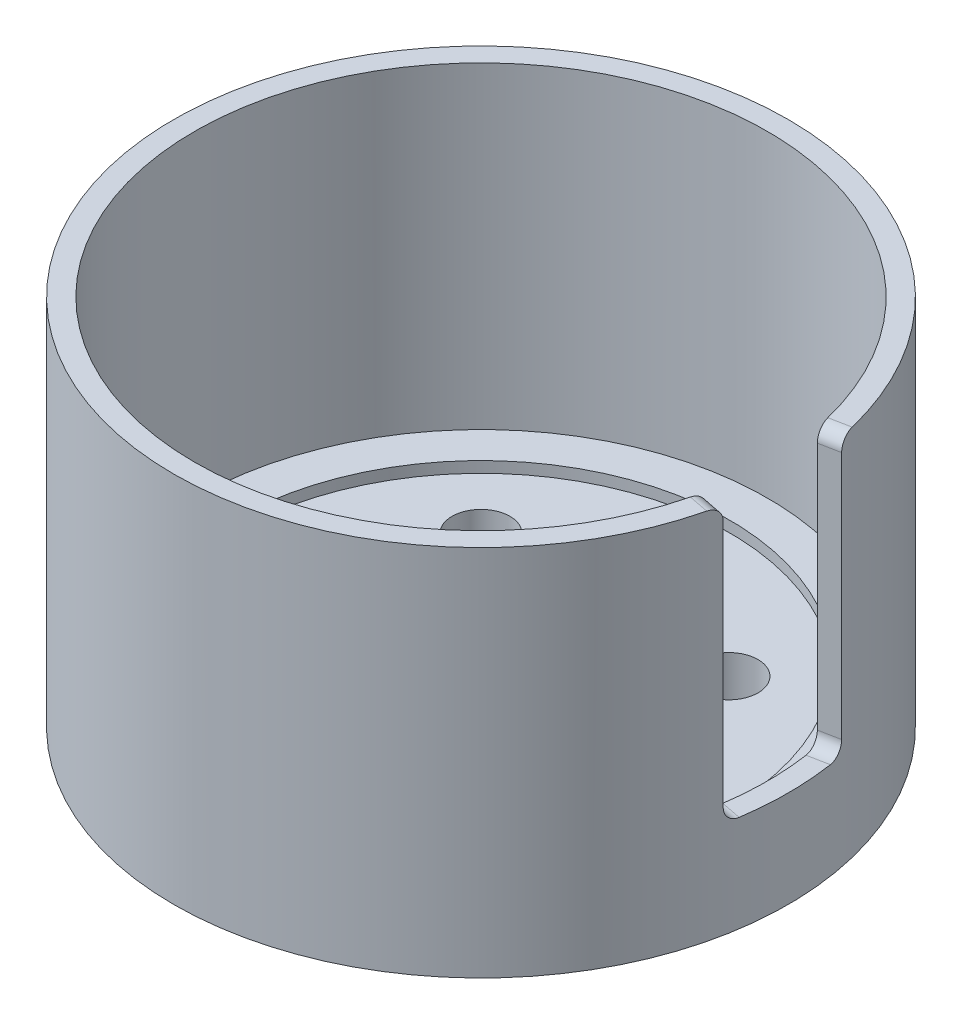
SolidWorks part; units mm, degrees
ref_plane "前视基准面" through (0, 0, 0) normal (0, 0, 1) x (1, 0, 0)
ref_plane "上视基准面" through (0, 0, 0) normal (0, 1, 0) x (1, 0, 0)
ref_plane "右视基准面" through (0, 0, 0) normal (1, 0, 0) x (0, 0, -1)
sketch "草图1" plane through (0, 0, 0) normal (0, 1, 0) x (1, 0, 0)
  circle A0 centre (0, 0) radius 22.25
  dimension "D1" = 44.5
extrude "凸台-拉伸1" add sketch "草图1" along normal blind 27
sketch "草图2" plane through (0, 27, 0) normal (0, 1, 0) x (1, 0, 0)
  circle A0 centre (0, 0) radius 20.75
  dimension "D1" = 41.5
extrude "切除-拉伸1" cut sketch "草图2" against normal blind 23
sketch "草图3" plane through (0, 4, 0) normal (0, 1, 0) x (1, 0, 0)
  circle A0 centre (0, 0) radius 18
  dimension "D1" = 36
extrude "切除-拉伸2" cut sketch "草图3" against normal blind 0.8
sketch "草图4" plane through (0, 0, 0) normal (0, 1, 0) x (1, 0, 0)
  line L0 (0, 0) -> (4.3576, 0) construction
  line L1 (0, 0) -> (0, 7.7921) construction
  line L2 (0, 0) -> (7.9484, 7.9484) construction
  line L3 (0, 0) -> (-3.3126, 3.3126) construction
  circle A0 centre (0, 0) radius 3.2
  circle A1 centre (-8.9803, 8.9803) radius 2.1
  circle A2 centre (8.9803, 8.9803) radius 2.1
  circle A3 centre (8.9803, -8.9803) radius 2.1
  circle A4 centre (-8.9803, -8.9803) radius 2.1
  circle A5 centre (0, 0) radius 12.7 construction
  dimension "D2" = 4.2
  dimension "D4" = 6.4
  dimension "D3" = 25.4
  dimension "D1" = 45
extrude "切除-拉伸4" cut sketch "草图4" along normal through all
sketch "草图5" plane through (0, 0, 0) normal (0, 1, 0) x (1, 0, 0)
  line L0 (20.3608, 4) -> (21.8327, 4.2892)
  line L1 (0, 0) -> (34.5288, 0) construction
  line L2 (20.3608, -4) -> (21.8327, -4.2892)
  line L3 (20.3608, -4) -> (20.3608, 4) construction
  arc A0 (20.3608, -4) -> (20.3608, 4) centre (0, 0) ccw
  arc A1 (21.8327, -4.2892) -> (21.8327, 4.2892) centre (0, 0) ccw
  dimension "D1" = 44.5
  dimension "D2" = 41.5
  dimension "D3" = 8
extrude "切除-拉伸5" cut sketch "草图5" against normal blind 20 from surface at 27 starting at face at (0, 27, 20.75)
fillet "圆角1" radius 1 1 edges at (21.0967, 27, -4.1446)
fillet "圆角2" radius 1 3 edges at (21.0967, 7, 4.1446) (21.0967, 7, -4.1446) (21.0967, 27, 4.1446)
sketch "草图6" plane through (0, 0, 0) normal (0, -1, 0) x (1, 0, 0)
  text T0 "<b>775-41.2</b>" font "微软雅黑" height 2
extrude "凸台-拉伸2" add sketch "草图6" along normal blind 0.6
